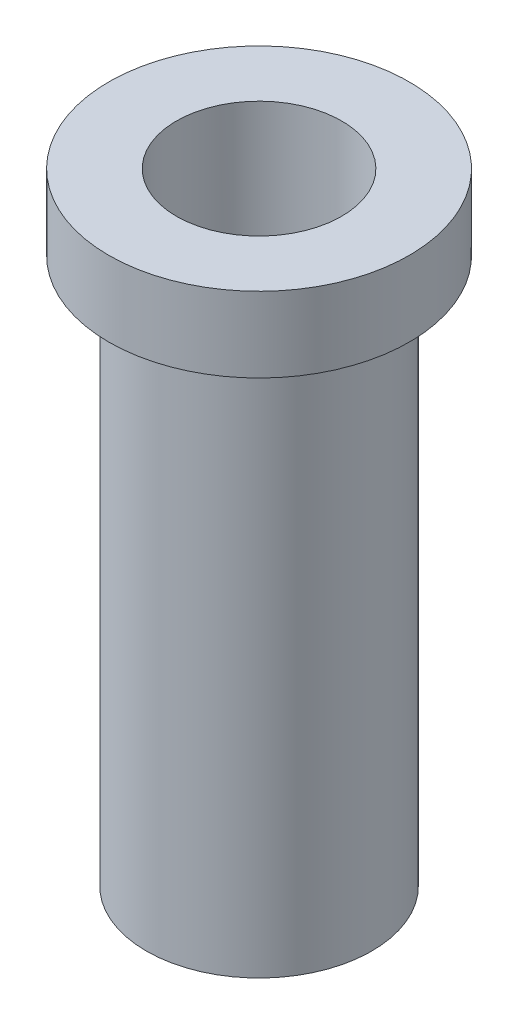
SolidWorks part; units mm, degrees
ref_plane "Front Plane" through (0, 0, 0) normal (0, 0, 1) x (1, 0, 0)
ref_plane "Top Plane" through (0, 0, 0) normal (0, 1, 0) x (1, 0, 0)
ref_plane "Right Plane" through (0, 0, 0) normal (1, 0, 0) x (0, 0, -1)
sketch "Sketch1" plane through (0, 0, 0) normal (0, 0, 1) x (1, 0, 0)
  line L0 (0, 0) -> (0, 36.3514)
  line L1 (0, 0) -> (7.5, 0)
  line L2 (0, 36.3514) -> (-2.5, 36.3514)
  line L3 (-2.5, 36.3514) -> (-2.5, 41.3514)
  line L4 (-2.5, 41.3514) -> (7.5, 41.3514)
  line L5 (7.5, 41.3514) -> (7.5, 0) construction
  line L6 (7.5, 0) -> (7.5, 41.3514)
revolve "Revolve1" add sketch "Sketch1" angle 360 about L5
sketch "Sketch2" plane through (0, 41.3514, 0) normal (0, 1, 0) x (1, 0, 0)
  circle A0 centre (7.5, 0) radius 5.5
extrude "Cut-Extrude1" cut sketch "Sketch2" against normal blind 45
